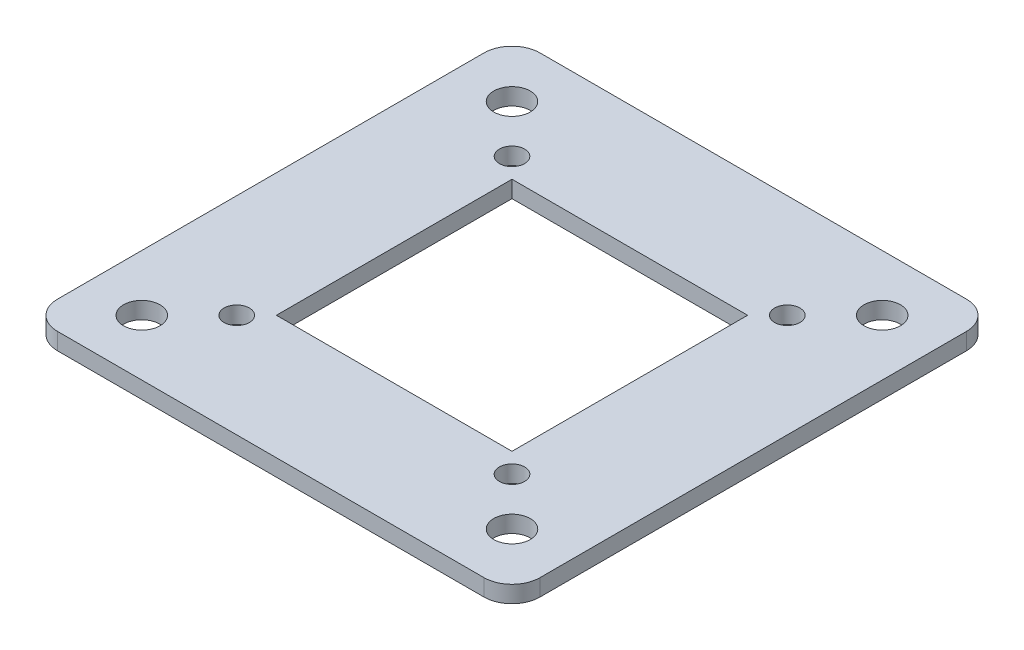
SolidWorks part; units mm, degrees
ref_plane "Front Plane" through (0, 0, 0) normal (0, 0, 1) x (1, 0, 0)
ref_plane "Top Plane" through (0, 0, 0) normal (0, 1, 0) x (1, 0, 0)
ref_plane "Right Plane" through (0, 0, 0) normal (1, 0, 0) x (0, 0, -1)
sketch "Sketch2" plane through (0, 0, 0) normal (0, 1, 0) x (1, 0, 0)
  line L1 (44.8549, -15.5885) -> (-41.1451, -15.5885)
  line L2 (44.8549, -15.5885) -> (44.8549, 70.4115)
  line L3 (44.8549, 70.4115) -> (-41.1451, 70.4115)
  line L4 (-41.1451, -15.5885) -> (-41.1451, 70.4115)
  line L5 (44.8549, -15.5885) -> (-41.1451, 70.4115) construction
  line L6 (44.8549, 70.4115) -> (-41.1451, -15.5885) construction
  line L7 (22.8549, 6.4115) -> (-19.1451, 6.4115)
  line L8 (22.8549, 6.4115) -> (22.8549, 48.4115)
  line L9 (22.8549, 48.4115) -> (-19.1451, 48.4115)
  line L10 (-19.1451, 6.4115) -> (-19.1451, 48.4115)
  line L11 (22.8549, 6.4115) -> (-19.1451, 48.4115) construction
  line L12 (22.8549, 48.4115) -> (-19.1451, 6.4115) construction
  point P0 (1.8549, 27.4115)
  point P5 (1.8549, 27.4115)
  dimension "D1" = 42
  dimension "D2" = 42
  dimension "D3" = 86
  dimension "D4" = 86
extrude "Boss-Extrude1" add sketch "Sketch2" along normal blind 3
sketch "Sketch3" plane through (0, 3, 0) normal (0, 1, 0) x (1, 0, 0)
  line L0 (44.8549, -15.5885) -> (34.8549, -15.5885) construction
  line L1 (-41.1451, -15.5885) -> (44.8549, -15.5885) construction
  line L2 (34.8549, -15.5885) -> (34.8549, -5.5885) construction
  line L3 (34.8549, -5.5885) -> (44.8549, -5.5885) construction
  line L4 (44.8549, -15.5885) -> (44.8549, 70.4115) construction
  line L5 (44.8549, 27.4115) -> (-41.1451, 27.4115) construction
  line L6 (-41.1451, 70.4115) -> (-41.1451, -15.5885) construction
  circle A0 centre (34.8549, -5.5885) radius 3.25
  circle A4 centre (-31.1451, -5.5885) radius 3.25
  circle A5 centre (-31.1451, 60.4115) radius 3.25
  circle A6 centre (34.8549, 60.4115) radius 3.25
  dimension "D1" = 10
  dimension "D2" = 10
  dimension "D3" = 2
extrude "Cut-Extrude1" cut sketch "Sketch3" against normal blind 3
sketch "Sketch7" plane through (0, 3, 0) normal (0, 1, 0) x (1, 0, 0)
  line L0 (22.8549, 6.4115) -> (26.3904, 2.876) construction
  line L1 (34.8549, -5.5885) -> (26.3904, 2.876) construction
  line L2 (1.8549, 70.4115) -> (1.8549, -15.5885) construction
  line L4 (44.8549, 27.4115) -> (-41.1451, 27.4115) construction
  line L5 (44.8549, -15.5885) -> (44.8549, 70.4115) construction
  line L6 (-41.1451, 70.4115) -> (-41.1451, -15.5885) construction
  line L7 (44.8549, 70.4115) -> (-41.1451, 70.4115) construction
  line L8 (-41.1451, -15.5885) -> (44.8549, -15.5885) construction
  circle A0 centre (26.3904, 2.876) radius 2.25
  circle A5 centre (-22.6807, 2.876) radius 2.25
  circle A6 centre (-22.6807, 51.947) radius 2.25
  circle A7 centre (26.3904, 51.947) radius 2.25
  dimension "D1" = 5
extrude "Cut-Extrude2" cut sketch "Sketch7" against normal blind 3
fillet "Fillet1" radius 5 1 edges at (-41.1451, 1.5, -70.4115)
fillet "Fillet2" radius 5 1 edges at (44.8549, 1.5, 15.5885)
fillet "Fillet3" radius 5 1 edges at (-41.1451, 1.5, 15.5885)
fillet "Fillet4" radius 5 1 edges at (44.8549, 1.5, -70.4115)
